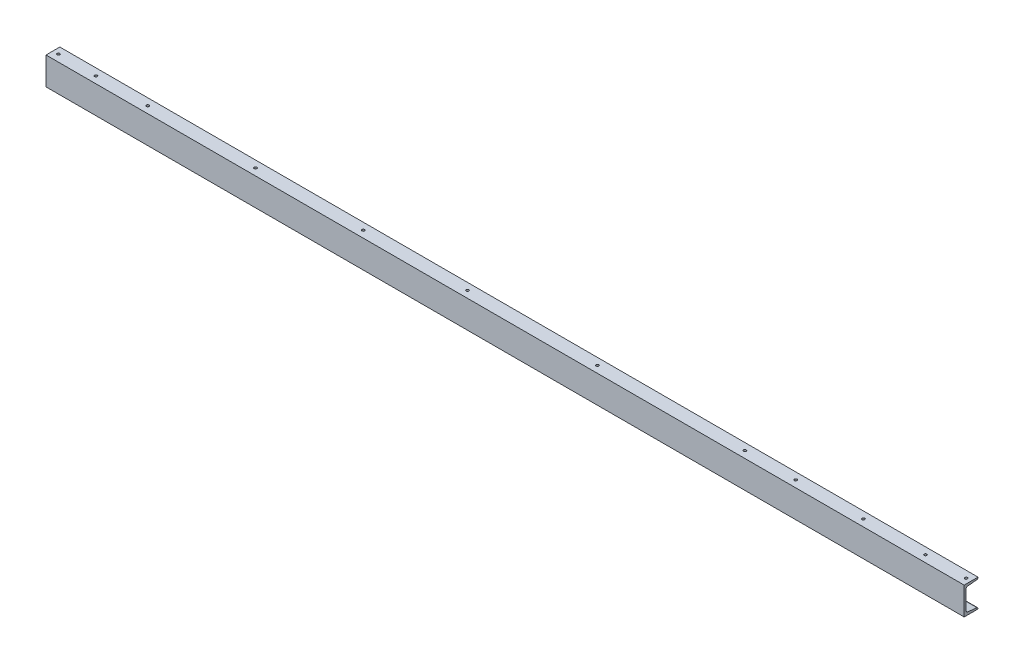
SolidWorks part; units mm, degrees
material "Plain Carbon Steel"
ref_plane "Front Plane" through (0, 0, 0) normal (0, 0, 1) x (1, 0, 0)
ref_plane "Top Plane" through (0, 0, 0) normal (0, 1, 0) x (1, 0, 0)
ref_plane "Right Plane" through (0, 0, 0) normal (1, 0, 0) x (0, 0, -1)
sketch "Sketch1" plane through (0, 0, 0) normal (0, 1, 0) x (1, 0, 0)
  line L0 (-530, 0) -> (2792, 0)
  dimension "D1" = 530
  dimension "D2" = 3322
other "Structural Member1"
ref_plane "Plane1" through (-530, 0, 0) normal (1, 0, 0) x (0, 0, -1)
sketch "Sketch16" plane through (-530, -50, 0) normal (1, 0, 0) x (0, 0, -1)
  line L0 (50, 100) -> (0, 100)
  line L1 (50, 0) -> (0, 0)
  line L2 (0, 100) -> (0, 0)
  line L6 (50, 100) -> (50, 98.3701)
  line L7 (50, 0) -> (50, 1.6299)
  line L12 (5.9, 82.48) -> (5.9, 17.52)
  line L17 (13.0638, 90.4362) -> (45.9704, 93.8948)
  line L18 (13.0638, 9.5638) -> (45.9704, 6.1052)
  arc A0 (45.9704, 93.8948) -> (50, 98.3701) centre (45.5, 98.3701) ccw
  arc A1 (45.9704, 6.1052) -> (50, 1.6299) centre (45.5, 1.6299) cw
  arc A9 (5.9, 17.52) -> (13.0638, 9.5638) centre (13.9, 17.52) ccw
  arc A10 (5.9, 82.48) -> (13.0638, 90.4362) centre (13.9, 82.48) cw
  point P8 (0, 50)
  point P9 (5.9, 50)
  point P10 (25, 100)
  point P11 (25, 0)
  point P12 (50, 5.6817)
  point P13 (50, 94.3183)
  point P14 (0, 0)
  dimension "D4" = 4.5
  dimension "RI" = 8
  dimension "D2" = 6
  dimension "D3" = 17.52
  dimension "Depth" = 100
  dimension "BF" = 50
  dimension "TW" = 5.9
  dimension "d1" = 64.96
sketch "Sketch12" plane through (0, 50, 0) normal (0, -1, 0) x (1, 0, 0)
  line L0 (-530, -50) -> (-530, 0) construction
  line L1 (2792, 0) -> (-530, 0) construction
  circle A0 centre (-510, -25) radius 4.7625
  circle A1 centre (-187, -25) radius 4.7625
  circle A2 centre (202.9, -25) radius 4.7625
  circle A3 centre (593, -25) radius 4.7625
  circle A4 centre (970, -25) radius 4.7625
  circle A5 centre (1440, -25) radius 4.7625
  circle A6 centre (-374.3, -25) radius 4.7625
  circle A7 centre (1973.8, -25) radius 4.7625
  circle A8 centre (2157.4, -25) radius 4.7625
  circle A9 centre (2402.5, -25) radius 4.7625
  circle A10 centre (2626.9, -25) radius 4.7625
  circle A11 centre (2774, -25) radius 4.7625
  dimension "D4" = 732.9
  dimension "D13" = 25
  dimension "D14" = 9.525
  dimension "D1" = 20
  dimension "D2" = 155.7
  dimension "D3" = 343
  dimension "D5" = 1123
  dimension "D6" = 1500
  dimension "D7" = 1970
  dimension "D8" = 2503.8
  dimension "D9" = 2687.4
  dimension "D10" = 2932.5
  dimension "D11" = 3156.9
  dimension "D12" = 3304
extrude "Cut-Extrude1" cut sketch "Sketch12" along normal blind 20
sketch "Sketch13" plane through (0, -29.6675, -5.9) normal (0, 0, -1) x (-1, 0, 0)
  line L0 (-2774, 71.3582) -> (-2774, 15.2756) construction
  line L1 (-2626.9, 71.3582) -> (-2626.9, 10.6225) construction
  line L2 (-2402.5, 71.3582) -> (-2402.5, 15.2756) construction
  line L3 (-2157.4, 71.3582) -> (-2157.4, 10.6225) construction
  line L4 (-1973.8, 71.3582) -> (-1973.8, 10.6225) construction
  line L5 (374.3, 71.3582) -> (374.3, 15.2756) construction
  line L6 (-1440, 71.3582) -> (-1440, 15.2756) construction
  line L7 (-970, 71.3582) -> (-970, 15.2756) construction
  line L8 (-593, 71.3582) -> (-593, 15.2756) construction
  line L9 (-202.9, 71.3582) -> (-202.9, 15.2756) construction
  line L10 (187, 71.3582) -> (187, 10.6225) construction
  line L11 (510, 71.3582) -> (510, 15.2756) construction
  line L12 (535.2313, 67.6675) -> (-2802.8557, 67.6675) construction
  line L13 (-2786.5, 67.6675) -> (-2761.5, 67.6675) construction
  line L14 (-2786.5, 72.6675) -> (-2761.5, 72.6675)
  line L15 (-2786.5, 62.6675) -> (-2761.5, 62.6675)
  line L16 (-2639.4, 67.6675) -> (-2614.4, 67.6675) construction
  line L17 (-2639.4, 72.6675) -> (-2614.4, 72.6675)
  line L18 (-2639.4, 62.6675) -> (-2614.4, 62.6675)
  line L19 (-2415, 67.6675) -> (-2390, 67.6675) construction
  line L20 (-2415, 72.6675) -> (-2390, 72.6675)
  line L21 (-2415, 62.6675) -> (-2390, 62.6675)
  line L22 (-2169.9, 67.6675) -> (-2144.9, 67.6675) construction
  line L23 (-2169.9, 72.6675) -> (-2144.9, 72.6675)
  line L24 (-2169.9, 62.6675) -> (-2144.9, 62.6675)
  line L25 (-1986.3, 67.6675) -> (-1961.3, 67.6675) construction
  line L26 (-1986.3, 72.6675) -> (-1961.3, 72.6675)
  line L27 (-1986.3, 62.6675) -> (-1961.3, 62.6675)
  line L28 (361.8, 67.6675) -> (386.8, 67.6675) construction
  line L29 (361.8, 72.6675) -> (386.8, 72.6675)
  line L30 (361.8, 62.6675) -> (386.8, 62.6675)
  line L31 (-1452.5, 67.6675) -> (-1427.5, 67.6675) construction
  line L32 (-1452.5, 72.6675) -> (-1427.5, 72.6675)
  line L33 (-1452.5, 62.6675) -> (-1427.5, 62.6675)
  line L34 (-982.5, 67.6675) -> (-957.5, 67.6675) construction
  line L35 (-982.5, 72.6675) -> (-957.5, 72.6675)
  line L36 (-982.5, 62.6675) -> (-957.5, 62.6675)
  line L37 (-605.5, 67.6675) -> (-580.5, 67.6675) construction
  line L38 (-605.5, 72.6675) -> (-580.5, 72.6675)
  line L39 (-605.5, 62.6675) -> (-580.5, 62.6675)
  line L40 (-215.4, 67.6675) -> (-190.4, 67.6675) construction
  line L41 (-215.4, 72.6675) -> (-190.4, 72.6675)
  line L42 (-215.4, 62.6675) -> (-190.4, 62.6675)
  line L43 (174.5, 67.6675) -> (199.5, 67.6675) construction
  line L44 (174.5, 72.6675) -> (199.5, 72.6675)
  line L45 (174.5, 62.6675) -> (199.5, 62.6675)
  line L46 (497.5, 67.6675) -> (522.5, 67.6675) construction
  line L47 (497.5, 72.6675) -> (522.5, 72.6675)
  line L48 (497.5, 62.6675) -> (522.5, 62.6675)
  line L50 (-2792, 79.6675) -> (530, 79.6675) construction
  arc A0 (-2786.5, 72.6675) -> (-2786.5, 62.6675) centre (-2786.5, 67.6675) ccw
  arc A1 (-2761.5, 62.6675) -> (-2761.5, 72.6675) centre (-2761.5, 67.6675) ccw
  arc A2 (-2639.4, 72.6675) -> (-2639.4, 62.6675) centre (-2639.4, 67.6675) ccw
  arc A3 (-2614.4, 62.6675) -> (-2614.4, 72.6675) centre (-2614.4, 67.6675) ccw
  arc A4 (-2415, 72.6675) -> (-2415, 62.6675) centre (-2415, 67.6675) ccw
  arc A5 (-2390, 62.6675) -> (-2390, 72.6675) centre (-2390, 67.6675) ccw
  arc A6 (-2169.9, 72.6675) -> (-2169.9, 62.6675) centre (-2169.9, 67.6675) ccw
  arc A7 (-2144.9, 62.6675) -> (-2144.9, 72.6675) centre (-2144.9, 67.6675) ccw
  arc A8 (-1986.3, 72.6675) -> (-1986.3, 62.6675) centre (-1986.3, 67.6675) ccw
  arc A9 (-1961.3, 62.6675) -> (-1961.3, 72.6675) centre (-1961.3, 67.6675) ccw
  arc A10 (361.8, 72.6675) -> (361.8, 62.6675) centre (361.8, 67.6675) ccw
  arc A11 (386.8, 62.6675) -> (386.8, 72.6675) centre (386.8, 67.6675) ccw
  arc A12 (-1452.5, 72.6675) -> (-1452.5, 62.6675) centre (-1452.5, 67.6675) ccw
  arc A13 (-1427.5, 62.6675) -> (-1427.5, 72.6675) centre (-1427.5, 67.6675) ccw
  arc A14 (-982.5, 72.6675) -> (-982.5, 62.6675) centre (-982.5, 67.6675) ccw
  arc A15 (-957.5, 62.6675) -> (-957.5, 72.6675) centre (-957.5, 67.6675) ccw
  arc A16 (-605.5, 72.6675) -> (-605.5, 62.6675) centre (-605.5, 67.6675) ccw
  arc A17 (-580.5, 62.6675) -> (-580.5, 72.6675) centre (-580.5, 67.6675) ccw
  arc A18 (-215.4, 72.6675) -> (-215.4, 62.6675) centre (-215.4, 67.6675) ccw
  arc A19 (-190.4, 62.6675) -> (-190.4, 72.6675) centre (-190.4, 67.6675) ccw
  arc A20 (174.5, 72.6675) -> (174.5, 62.6675) centre (174.5, 67.6675) ccw
  arc A21 (199.5, 62.6675) -> (199.5, 72.6675) centre (199.5, 67.6675) ccw
  arc A22 (497.5, 72.6675) -> (497.5, 62.6675) centre (497.5, 67.6675) ccw
  arc A23 (522.5, 62.6675) -> (522.5, 72.6675) centre (522.5, 67.6675) ccw
  ellipse E12 centre (-2774, 71.3582) end of major axis (-2778.7625, 71.3582) minor radius 0.5006 construction
  ellipse E13 centre (-2626.9, 71.3582) end of major axis (-2631.6625, 71.3582) minor radius 0.5006 construction
  ellipse E14 centre (-2402.5, 71.3582) end of major axis (-2407.2625, 71.3582) minor radius 0.5006 construction
  ellipse E15 centre (-2157.4, 71.3582) end of major axis (-2162.1625, 71.3582) minor radius 0.5006 construction
  ellipse E16 centre (-1973.8, 71.3582) end of major axis (-1978.5625, 71.3582) minor radius 0.5006 construction
  ellipse E17 centre (374.3, 71.3582) end of major axis (369.5375, 71.3582) minor radius 0.5006 construction
  ellipse E18 centre (-1440, 71.3582) end of major axis (-1444.7625, 71.3582) minor radius 0.5006 construction
  ellipse E19 centre (-970, 71.3582) end of major axis (-974.7625, 71.3582) minor radius 0.5006 construction
  ellipse E20 centre (-593, 71.3582) end of major axis (-597.7625, 71.3582) minor radius 0.5006 construction
  ellipse E21 centre (-202.9, 71.3582) end of major axis (-207.6625, 71.3582) minor radius 0.5006 construction
  ellipse E22 centre (187, 71.3582) end of major axis (182.2375, 71.3582) minor radius 0.5006 construction
  ellipse E23 centre (510, 71.3582) end of major axis (505.2375, 71.3582) minor radius 0.5006 construction
  point P0 (-2774, 71.3582)
  point P9 (-2626.9, 71.3582)
  point P18 (-2402.5, 71.3582)
  point P27 (-2157.4, 71.3582)
  point P36 (-1973.8, 71.3582)
  point P45 (374.3, 71.3582)
  point P54 (-1440, 71.3582)
  point P63 (-970, 71.3582)
  point P72 (-593, 71.3582)
  point P81 (-202.9, 71.3582)
  point P90 (187, 71.3582)
  point P99 (510, 71.3582)
  point P110 (-2774, 67.6675)
  point P111 (-2626.9, 67.6675)
  point P112 (-2402.5, 67.6675)
  point P113 (-2157.4, 67.6675)
  point P114 (-1973.8, 67.6675)
  point P115 (374.3, 67.6675)
  point P116 (-1440, 67.6675)
  point P117 (-970, 67.6675)
  point P118 (-593, 67.6675)
  point P119 (-202.9, 67.6675)
  point P120 (187, 67.6675)
  point P121 (510, 67.6675)
  point P124 (-2774, 67.6675)
  point P131 (-2626.9, 67.6675)
  point P138 (-2402.5, 67.6675)
  point P145 (-2157.4, 67.6675)
  point P152 (-1973.8, 67.6675)
  point P159 (374.3, 67.6675)
  point P166 (-1440, 67.6675)
  point P173 (-970, 67.6675)
  point P180 (-593, 67.6675)
  point P187 (-202.9, 67.6675)
  point P194 (187, 67.6675)
  point P201 (510, 67.6675)
  dimension "D1" = 5
  dimension "D2" = 25
  dimension "D3" = 12
extrude "Cut-Extrude2" cut sketch "Sketch13" along normal blind 40
sketch "Sketch14" plane through (0, -50, 0) normal (0, -1, 0) x (1, 0, 0)
  circle A0 centre (-5, -25) radius 4.7625
  circle A1 centre (2295, -25) radius 4.7625
extrude "Cut-Extrude3" cut sketch "Sketch14" against normal blind 20
sketch "Sketch15" plane through (0, -29.6675, -5.9) normal (0, 0, -1) x (-1, 0, 0)
  line L0 (-2295, -12.0232) -> (-2295, -7.2392) construction
  line L1 (5, -12.0232) -> (5, -7.2392) construction
  line L2 (30.2471, -8.3325) -> (-2322.2333, -8.3325) construction
  line L4 (-7.5, -8.3325) -> (17.5, -8.3325) construction
  line L5 (-7.5, -3.3325) -> (17.5, -3.3325)
  line L6 (-7.5, -13.3325) -> (17.5, -13.3325)
  line L7 (-2307.5, -8.3325) -> (-2282.5, -8.3325) construction
  line L8 (-2307.5, -3.3325) -> (-2282.5, -3.3325)
  line L9 (-2307.5, -13.3325) -> (-2282.5, -13.3325)
  line L10 (-2792, -20.3325) -> (530, -20.3325) construction
  arc A0 (-7.5, -3.3325) -> (-7.5, -13.3325) centre (-7.5, -8.3325) ccw
  arc A1 (17.5, -13.3325) -> (17.5, -3.3325) centre (17.5, -8.3325) ccw
  arc A2 (-2307.5, -3.3325) -> (-2307.5, -13.3325) centre (-2307.5, -8.3325) ccw
  arc A3 (-2282.5, -13.3325) -> (-2282.5, -3.3325) centre (-2282.5, -8.3325) ccw
  ellipse E0 centre (-2295, -12.0232) end of major axis (-2290.2375, -12.0232) minor radius 0.5006 construction
  ellipse E2 centre (5, -12.0232) end of major axis (9.7625, -12.0232) minor radius 0.5006 construction
  point P0 (-2295, -12.0232)
  point P9 (5, -12.0232)
  point P22 (-2295, -8.3325)
  point P23 (5, -8.3325)
  point P26 (5, -8.3325)
  point P33 (-2295, -8.3325)
  dimension "D3" = 5
  dimension "D1" = 12
  dimension "D2" = 25
extrude "Cut-Extrude4" cut sketch "Sketch15" along normal blind 40
